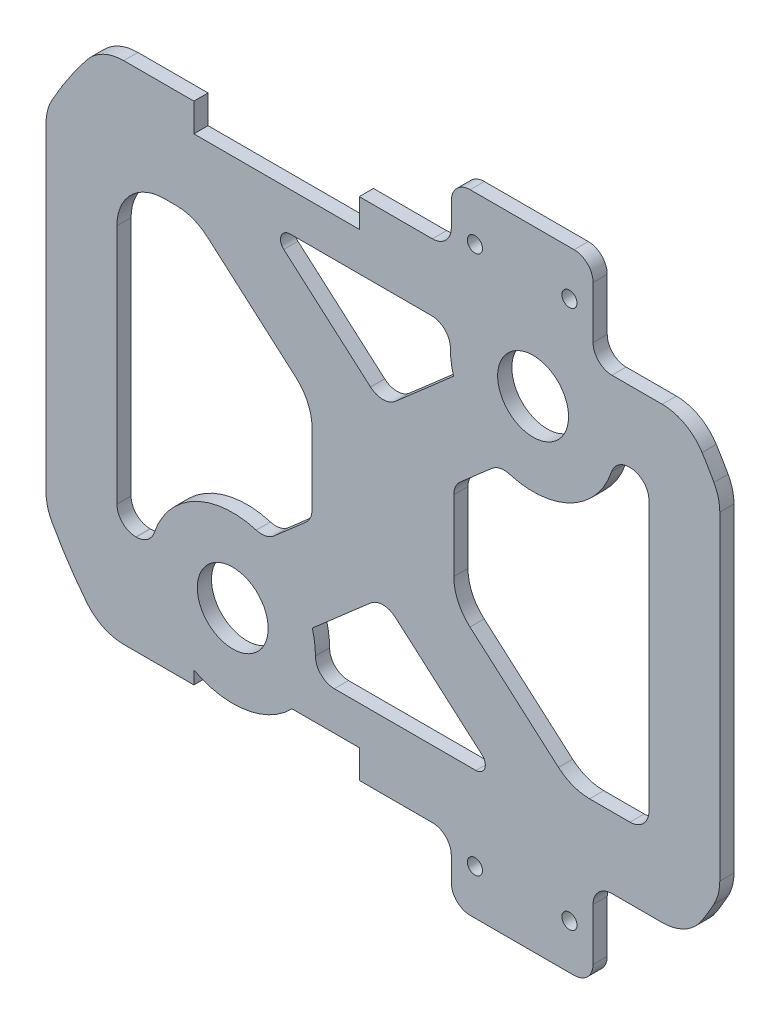
SolidWorks part; units mm, degrees
material "Acrílico (médio-alto impacto)"
ref_plane "Plano frontal" through (0, 0, 0) normal (0, 0, 1) x (1, 0, 0)
ref_plane "Plano superior" through (0, 0, 0) normal (0, 1, 0) x (1, 0, 0)
ref_plane "Plano direito" through (0, 0, 0) normal (1, 0, 0) x (0, 0, -1)
sketch "Esboço1" plane through (0, 0, 0) normal (0, 0, 1) x (1, 0, 0)
  line L0 (80, 0) -> (0, 0) construction
  line L1 (-80, -66.5) -> (80, -66.5)
  line L2 (-80, -66.5) -> (-80, 66.5)
  line L3 (-80, 66.5) -> (80, 66.5)
  line L4 (80, -66.5) -> (80, 66.5)
  line L5 (-80, -66.5) -> (80, 66.5) construction
  line L6 (-80, 66.5) -> (80, -66.5) construction
  line L7 (80, 47.5) -> (-80, 47.5) construction
  line L8 (80, -47.5) -> (-80, -47.5) construction
  line L9 (14.4719, 66.5) -> (14.4719, 53.5)
  line L10 (0, 0) -> (0, 66.5) construction
  line L11 (44.4719, 66.5) -> (44.4719, 47.5)
  line L12 (-5.0035, -47.5) -> (-40.0035, -47.5)
  line L13 (14.4719, -66.5) -> (14.4719, -53.5)
  line L14 (44.4719, 47.5) -> (64.372, 47.5)
  line L15 (28.6277, 47.5) -> (28.6277, 66.5) construction
  line L16 (14.4719, 53.5) -> (-59.479, 53.5)
  line L17 (-40.0035, -53.5) -> (-40.0035, -47.5)
  line L18 (-31.7837, -35.2994) -> (31.7837, 35.2994) construction
  line L24 (-56.2917, 32.5) -> (-39.9802, 32.5)
  line L25 (-39.9802, 32.5) -> (-15, 10.6848)
  line L30 (-15, 10.6848) -> (-15, -10.6848)
  line L31 (-39.9802, -32.5) -> (-15, -10.6848)
  line L36 (-56.2917, -32.5) -> (-39.9802, -32.5)
  line L37 (56.2917, 32.5) -> (39.9802, 32.5)
  line L57 (39.9802, 32.5) -> (15, 10.6848)
  line L58 (15, 10.6848) -> (15, -10.6848)
  line L59 (39.9802, -32.5) -> (15, -10.6848)
  line L60 (56.2917, -32.5) -> (39.9802, -32.5)
  line L61 (-25, -39.3325) -> (0, -17.5)
  line L63 (-25, -39.3325) -> (25, -39.3325)
  line L64 (25, -39.3325) -> (0, -17.5)
  line L65 (-25, 39.3325) -> (0, 17.5)
  line L66 (25, 39.3325) -> (0, 17.5)
  line L67 (-25, 39.3325) -> (25, 39.3325)
  line L69 (-5.0035, -53.5) -> (-40.0035, -53.5)
  line L70 (-5.0035, 53.5) -> (-40.0035, 53.5)
  line L71 (-5.0035, 53.5) -> (-5.0035, 47.5)
  line L72 (-5.0035, 47.5) -> (-40.0035, 47.5)
  line L73 (-40.0035, 53.5) -> (-40.0035, 47.5)
  line L74 (-5.0035, 53.5) -> (-40.0035, 47.5) construction
  line L75 (-5.0035, 47.5) -> (-40.0035, 53.5) construction
  line L76 (-5.0035, -53.5) -> (-5.0035, -47.5)
  line L77 (14.4719, -53.5) -> (-59.479, -53.5)
  line L78 (44.4719, -66.5) -> (44.4719, -47.5)
  line L79 (44.4719, -47.5) -> (64.372, -47.5)
  line L80 (-71.2917, -36.2974) -> (-71.2917, 36.2974)
  line L81 (-56.2917, 32.5) -> (-56.2917, -32.5)
  line L82 (56.2917, 32.5) -> (56.2917, -32.5)
  line L83 (71.2917, -36.2974) -> (71.2917, 36.2974)
  circle A0 centre (0, 0) radius 80
  circle A1 centre (-31.7837, -35.2994) radius 7.5
  circle A2 centre (31.7837, 35.2994) radius 7.5
  circle A3 centre (19.4719, 57) radius 1.6
  circle A8 centre (19.4719, -57) radius 1.6
  arc A9 (-56.2917, -32.5) -> (-56.2917, 32.5) centre (0, 0) cw
  arc A11 (56.2917, -32.5) -> (56.2917, 32.5) centre (0, 0) ccw
  circle A12 centre (-31.7837, -35.2994) radius 17.5
  circle A13 centre (31.7837, 35.2994) radius 17.5
  circle A14 centre (39.4719, 57) radius 1.6
  circle A15 centre (39.4719, -57) radius 1.6
  point P0 (0, 0)
  point P37 (-22.5035, 50.5)
  point P38 (28.6277, 57)
  point P45 (-65, 0)
  point P65 (-22.5035, 53.5)
  dimension "D6" = 15
  dimension "D7" = 3.2
  dimension "D18" = 15
  dimension "D9" = 15
  dimension "D11" = 35
  dimension "D1" = 95
  dimension "D2" = 19
  dimension "D3" = 160
  dimension "D4" = 95
  dimension "D5" = 48
  dimension "D8" = 15
  dimension "D10" = 30
  dimension "D12" = 30
  dimension "D13" = 35
  dimension "D14" = 5
  dimension "D15" = 50
  dimension "D16" = 5
  dimension "D17" = 6
  dimension "D19" = 35
  dimension "D21" = 15
extrude "Ressalto-extrusão1" add sketch "Esboço1" along normal blind 3
fillet "Filete2" radius 10 13 edges at (39.9802, -32.5, 1.5) (15, -10.6848, 1.5) (-15, 10.6848, 1.5) (-39.9802, 32.5, 1.5) (-71.2917, -36.2974, 1.5) (-71.2917, 36.2974, 1.5) (-56.2917, 32.5, 1.5) (71.2917, 36.2974, 1.5) (71.2917, -36.2974, 1.5) (64.372, 47.5, 1.5) (64.372, -47.5, 1.5) (-59.479, 53.5, 1.5) (-59.479, -53.5, 1.5)
fillet "Filete3" radius 4 21 edges at (49.0584, 32.5, 1.5) (24.8078, 19.2499, 1.5) (15, 10.6848, 1.5) (-15, -10.6848, 1.5) (-24.8078, -19.2499, 1.5) (-49.0584, -32.5, 1.5) (14.7548, 39.3325, 1.5) (0, 17.5, 1.5) (0, -17.5, 1.5) (-14.7548, -39.3325, 1.5) (14.4719, 53.5, 1.5) (14.4719, -53.5, 1.5) (44.4719, -47.5, 1.5) (44.4719, 47.5, 1.5) (14.4719, -66.5, 1.5) (14.4719, 66.5, 1.5) (44.4719, 66.5, 1.5) (44.4719, -66.5, 1.5) (-56.2917, -32.5, 1.5) (56.2917, 32.5, 1.5) (56.2917, -32.5, 1.5)
fillet "Filete4" radius 2 2 edges at (25, -39.3325, 1.5) (-25, 39.3325, 1.5)
